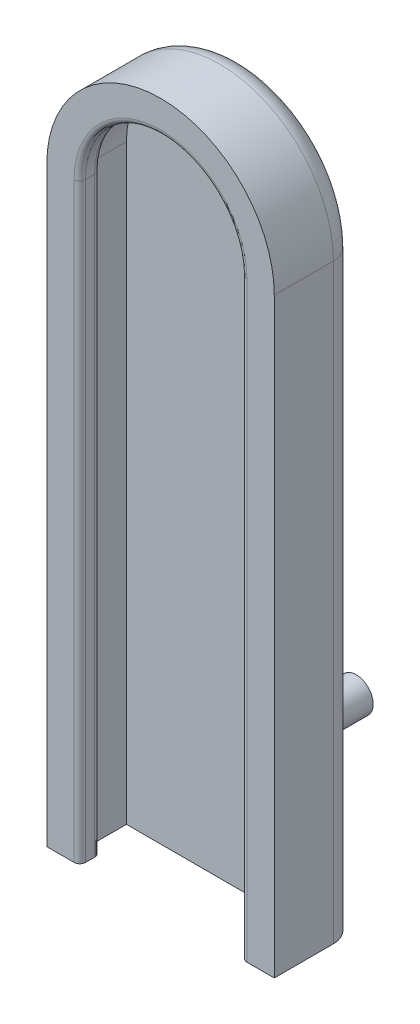
SolidWorks part; units mm, degrees
ref_plane "Front Plane" through (0, 0, 0) normal (0, 0, 1) x (1, 0, 0)
ref_plane "Top Plane" through (0, 0, 0) normal (0, 1, 0) x (1, 0, 0)
ref_plane "Right Plane" through (0, 0, 0) normal (1, 0, 0) x (0, 0, -1)
sketch "Sketch1" plane through (0, 0, 0) normal (0, 0, 1) x (1, 0, 0)
  line L0 (0, 26) -> (10, 26)
  line L1 (0, 0) -> (10, 0)
  line L2 (0, 0) -> (0, 26)
  line L4 (10, 0) -> (10, 26)
extrude "Boss-Extrude1" add sketch "Sketch1" along normal blind 1
sketch "Sketch2" plane through (0, 0, 0) normal (0, 0, -1) x (-1, 0, 0)
  line L0 (-10, 26) -> (0, 26) construction
  line L1 (-10, 0) -> (-10, 26) construction
  line L2 (-10, 26) -> (0, 26)
  arc A0 (0, 26) -> (-10, 26) centre (-5, 26) ccw
extrude "Boss-Extrude5" add sketch "Sketch2" against normal blind 3.6
sketch "Sketch6" plane through (0, 0, 0) normal (0, -1, 0) x (1, 0, 0)
  line L0 (0, 1) -> (0, 3.6)
  line L3 (10, 1) -> (10, 3.6)
  line L4 (0, 3.6) -> (1.45, 3.6)
  line L5 (10, 3.6) -> (8.55, 3.6)
  line L6 (1.45, 3.6) -> (1.45, 1)
  line L7 (8.55, 3.6) -> (8.55, 1)
  line L8 (0, 1) -> (10, 1) construction
  line L9 (1.45, 1) -> (0, 1)
  line L10 (8.55, 1) -> (10, 1)
  line L11 (0, 3.6) -> (0, 1) construction
  line L12 (10, 3.6) -> (10, 1) construction
extrude "Boss-Extrude9" add sketch "Sketch6" against normal up to vertex (26 mm away)
sketch "Sketch7" plane through (0, 0, 0) normal (0, -1, 0) x (1, 0, 0)
  line L1 (1.45, 1) -> (0.9, 1)
  line L2 (1.45, 1) -> (1.45, 2.7)
  line L3 (1.45, 2.7) -> (0.9, 2.7)
  line L4 (0.9, 1) -> (0.9, 2.7)
  line L5 (8.55, 1) -> (9.1, 1)
  line L6 (8.55, 1) -> (8.55, 2.7)
  line L7 (8.55, 2.7) -> (9.1, 2.7)
  line L8 (9.1, 1) -> (9.1, 2.7)
extrude "Cut-Extrude1" cut sketch "Sketch7" against normal blind 26
sketch "Sketch10" plane through (0, 0, 3.6) normal (0, 0, 1) x (1, 0, 0)
  line L0 (8.55, 26) -> (1.45, 26) construction
  line L1 (1.45, 26) -> (1.45, 0) construction
  line L2 (1.45, 26) -> (8.55, 26)
  arc A0 (8.55, 26) -> (1.45, 26) centre (5, 26) ccw
extrude "Cut-Extrude3" cut sketch "Sketch10" against normal up to vertex (0.9 mm away)
sketch "Sketch11" plane through (0, 0, 1) normal (0, 0, 1) x (1, 0, 0)
  line L0 (0.9, 26) -> (9.1, 26)
  line L1 (0.9, 26) -> (0.9, 0) construction
  arc A0 (0.9, 26) -> (9.1, 26) centre (5, 26) cw
extrude "Cut-Extrude4" cut sketch "Sketch11" along normal up to vertex (1.7 mm away) up to point (1.45, 26, 2.7)
fillet "Fillet1" radius 0.25 6 edges at (8.55, 13, 2.7) (5, 29.55, 2.7) (1.45, 13, 3.6) (5, 29.55, 3.6) (1.45, 13, 2.7) (8.55, 13, 3.6)
fillet "Fillet2" radius 1 3 edges at (0, 13, 0) (5, 31, 0) (10, 13, 0)
sketch "Sketch12" plane through (0, 0, 0) normal (0, 0, -1) x (-1, 0, 0)
  circle A0 centre (-5, 4) radius 0.75
extrude "Boss-Extrude10" add sketch "Sketch12" along normal blind 5
